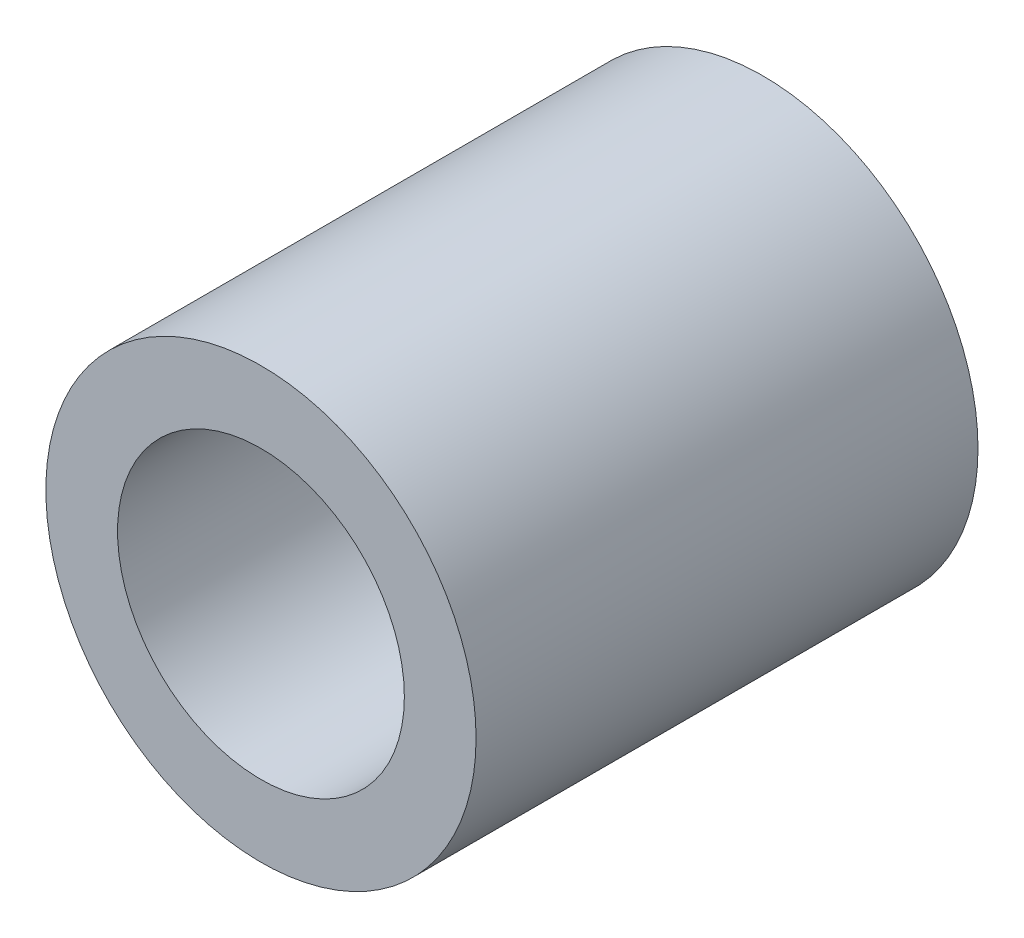
SolidWorks part; units mm, degrees
ref_plane "Plan de face" through (0, 0, 0) normal (0, 0, 1) x (1, 0, 0)
ref_plane "Plan de dessus" through (0, 0, 0) normal (0, 1, 0) x (1, 0, 0)
ref_plane "Plan de droite" through (0, 0, 0) normal (1, 0, 0) x (0, 0, -1)
sketch "Esquisse1" plane through (0, 0, 0) normal (0, 0, 1) x (1, 0, 0)
  circle A0 centre (0, 0) radius 1
  circle A1 centre (0, 0) radius 1.5
  dimension "D1" = 3
  dimension "D2" = 2
extrude "Boss.-Extru.1" add sketch "Esquisse1" along normal blind 3.5
